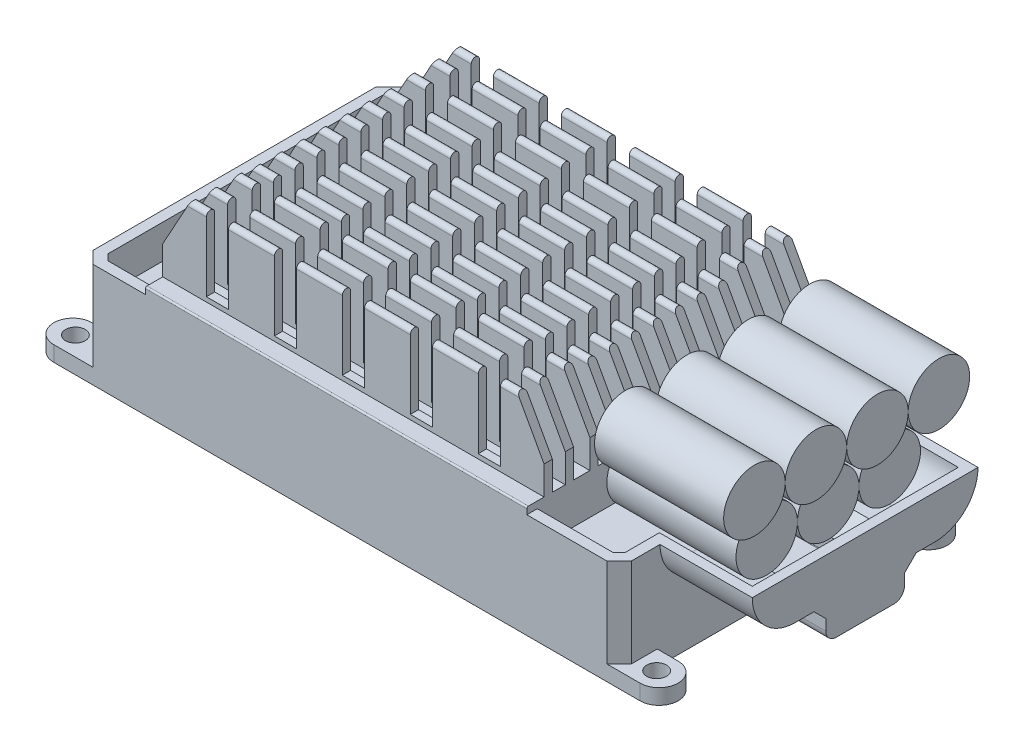
SolidWorks part; units mm, degrees
ref_plane "Front Plane" through (0, 0, 0) normal (0, 0, 1) x (1, 0, 0)
ref_plane "Top Plane" through (0, 0, 0) normal (0, 1, 0) x (1, 0, 0)
ref_plane "Right Plane" through (0, 0, 0) normal (1, 0, 0) x (0, 0, -1)
sketch "Sketch1" plane through (0, 0, 0) normal (0, 1, 0) x (1, 0, 0)
  line L1 (-43.75, -25) -> (43.75, -25)
  line L2 (-43.75, -25) -> (-43.75, 25)
  line L3 (-43.75, 25) -> (43.75, 25)
  line L4 (43.75, -25) -> (43.75, 25)
  line L5 (-43.75, -25) -> (43.75, 25) construction
  line L6 (-43.75, 25) -> (43.75, -25) construction
  point P0 (0, 0)
  dimension "D1" = 87.5
  dimension "D2" = 50
extrude "Boss-Extrude1" add sketch "Sketch1" along normal blind 17
sketch "Sketch2" plane through (0, 0, 0) normal (0, -1, 0) x (1, 0, 0)
  line L0 (43.75, 25) -> (47.15, 25)
  line L1 (47.15, 18.8) -> (43.75, 18.8)
  line L2 (43.75, 25) -> (43.75, -25) construction
  line L3 (43.75, 18.8) -> (43.75, 25)
  line L4 (50.25, 25.3121) -> (50.25, 13.6499) construction
  line L5 (-43.75, 25) -> (-48.15, 25)
  line L6 (-48.15, 18.8) -> (-43.75, 18.8)
  line L7 (-43.75, -25) -> (-43.75, 25) construction
  line L8 (-43.75, 18.8) -> (-43.75, 25)
  line L9 (-51.25, 27.9542) -> (-51.25, 11.7767) construction
  line L10 (-0.5, 36.3188) -> (-0.5, -36.8668) construction
  line L11 (-48.15, 21.9) -> (47.15, 21.9) construction
  arc A0 (47.15, 25) -> (47.15, 18.8) centre (47.15, 21.9) cw
  circle A1 centre (46.75, 21.9) radius 1.6
  arc A2 (-48.15, 25) -> (-48.15, 18.8) centre (-48.15, 21.9) ccw
  circle A3 centre (-47.75, 21.9) radius 1.6
  dimension "D3" = 94.5
  dimension "D5" = 3.2
  dimension "D1" = 6.2
  dimension "D2" = 6.5
  dimension "D4" = 7.5
extrude "Boss-Extrude2" add sketch "Sketch2" against normal blind 2.5
mirror "Mirror5" about plane through (0, 0, 0) normal (0, 0, 1) of "Boss-Extrude2"
chamfer "Chamfer1" distance 2 angle 45 4 edges at (-43.75, 9.75, -25) (43.75, 9.75, -25)
ref_plane "Plane1" through (-33.25, 0, 0) normal (-1, 0, 0) x (0, 0, 1)
sketch "Sketch3" plane through (-33.25, 0, 0) normal (-1, 0, 0) x (0, 0, 1)
  line L0 (-25, 17) -> (0, 17)
  line L1 (0, 17) -> (0, 30.1)
  line L2 (-0.675, 29.425) -> (-0.675, 18.1)
  line L3 (-0.675, 18.1) -> (-2.9, 18.1)
  line L4 (-2.9, 18.1) -> (-2.9, 29.425)
  line L5 (-4.25, 29.425) -> (-4.25, 18.1)
  line L6 (-4.25, 18.1) -> (-6.45, 18.1)
  line L7 (-6.45, 18.1) -> (-6.45, 29.425)
  line L8 (-7.8, 29.425) -> (-7.8, 18.1)
  line L9 (-7.8, 18.1) -> (-9.95, 18.1)
  line L10 (-9.95, 18.1) -> (-9.95, 29.425)
  line L11 (-11.3, 29.425) -> (-11.3, 18.1)
  line L12 (-11.3, 18.1) -> (-13.4, 18.1)
  line L13 (-13.4, 18.1) -> (-13.4, 30.075)
  line L14 (-14.75, 30.075) -> (-14.75, 18.1)
  line L15 (-14.75, 18.1) -> (-17.4, 18.1)
  line L16 (-17.4, 18.1) -> (-17.4, 30.075)
  line L17 (-18.75, 30.075) -> (-18.75, 18.1)
  line L18 (-18.75, 18.1) -> (-20.85, 18.1)
  line L19 (-20.85, 18.1) -> (-20.85, 30.075)
  line L20 (-22.2, 30.075) -> (-22.2, 18.1)
  line L21 (-22.2, 18.1) -> (-24.75, 18.1)
  line L22 (-25, 17.85) -> (-25, 17)
  line L23 (-22.2, 18.1) -> (-20.85, 18.1) construction
  line L24 (-18.75, 18.1) -> (-17.4, 18.1) construction
  line L25 (-14.75, 18.1) -> (-13.4, 18.1) construction
  line L26 (-11.3, 18.1) -> (-9.95, 18.1) construction
  line L27 (-7.8, 18.1) -> (-6.45, 18.1) construction
  line L28 (-4.25, 18.1) -> (-2.9, 18.1) construction
  line L29 (-23, 17) -> (23, 17) construction
  line L30 (-25, 2.5) -> (-25, 17) construction
  line L31 (0, 32.3673) -> (0, 1.3206) construction
  line L32 (25, 17) -> (25, 2.5) construction
  line L33 (-29.0745, 30.75) -> (-4.8916, 30.75) construction
  line L34 (-29.5054, 30.1) -> (10.134, 30.1) construction
  arc A0 (0, 30.1) -> (-0.675, 29.425) centre (0, 29.425) ccw
  arc A1 (-2.9, 29.425) -> (-4.25, 29.425) centre (-3.575, 29.425) ccw
  arc A2 (-6.45, 29.425) -> (-7.8, 29.425) centre (-7.125, 29.425) ccw
  arc A3 (-9.95, 29.425) -> (-11.3, 29.425) centre (-10.625, 29.425) ccw
  arc A4 (-13.4, 30.075) -> (-14.75, 30.075) centre (-14.075, 30.075) ccw
  arc A5 (-17.4, 30.075) -> (-18.75, 30.075) centre (-18.075, 30.075) ccw
  arc A6 (-20.85, 30.075) -> (-22.2, 30.075) centre (-21.525, 30.075) ccw
  arc A7 (-24.75, 18.1) -> (-25, 17.85) centre (-24.75, 17.85) ccw
  dimension "D10" = 0.25
  dimension "D1" = 2.8
  dimension "D2" = 4.8
  dimension "D3" = 1.35
  dimension "D4" = 0.675
  dimension "D5" = 8.8
  dimension "D6" = 12.25
  dimension "D7" = 15.75
  dimension "D8" = 19.3
  dimension "D9" = 1.1
  dimension "D11" = 12.65
  dimension "D12" = 12
extrude "Boss-Extrude3" add sketch "Sketch3" against normal blind 62
mirror "Mirror3" about plane through (0, 0, 0) normal (0, 0, 1) of "Boss-Extrude3"
sketch "Sketch4" plane through (0, 0, -22.2) normal (0, 0, -1) x (-1, 0, 0)
  line L0 (28.85, 30.75) -> (33.25, 22.75)
  line L1 (33.25, 22.75) -> (33.25, 30.75)
  line L2 (33.25, 30.75) -> (28.85, 30.75)
  line L3 (33.25, 30.075) -> (33.25, 18.1) construction
  line L4 (33.25, 30.75) -> (-28.75, 30.75) construction
  line L5 (-28.75, 22.75) -> (-24.35, 30.75)
  line L6 (-24.35, 30.75) -> (-28.75, 30.75)
  line L7 (-28.75, 30.75) -> (-28.75, 22.75)
  line L8 (-28.75, 30.075) -> (-28.75, 18.1) construction
  line L9 (-28.75, 18.1) -> (33.25, 18.1) construction
  line L10 (-21.65, 30.75) -> (-18.05, 30.75)
  line L11 (-21.65, 30.75) -> (-21.65, 18.85)
  line L12 (-21.65, 18.85) -> (-18.05, 18.85)
  line L13 (-18.05, 30.75) -> (-18.05, 18.85)
  line L14 (-10.6, 30.75) -> (-10.6, 18.85)
  line L15 (-10.6, 30.75) -> (-7, 30.75)
  line L16 (-7, 30.75) -> (-7, 18.85)
  line L17 (-10.6, 18.85) -> (-7, 18.85)
  line L18 (0.45, 30.75) -> (0.45, 18.85)
  line L19 (0.45, 30.75) -> (4.05, 30.75)
  line L20 (4.05, 30.75) -> (4.05, 18.85)
  line L21 (0.45, 18.85) -> (4.05, 18.85)
  line L22 (11.5, 30.75) -> (11.5, 18.85)
  line L23 (11.5, 30.75) -> (15.1, 30.75)
  line L24 (15.1, 30.75) -> (15.1, 18.85)
  line L25 (11.5, 18.85) -> (15.1, 18.85)
  line L26 (22.55, 30.75) -> (22.55, 18.85)
  line L27 (22.55, 30.75) -> (26.15, 30.75)
  line L28 (26.15, 30.75) -> (26.15, 18.85)
  line L29 (22.55, 18.85) -> (26.15, 18.85)
  dimension "D1" = 4.4
  dimension "D2" = 8
  dimension "D3" = 7.1
  dimension "D4" = 3.6
  dimension "D5" = 0.75
  dimension "D7" = 7.1
  dimension "D6" = 5
extrude "Cut-Extrude1" cut sketch "Sketch4" against normal through all both and the other way through all
sketch "Sketch5" plane through (43.75, 0, 0) normal (1, 0, 0) x (0, 0, -1)
  line L0 (0, 4.6) -> (0, 17)
  line L1 (-23, 17) -> (23, 17) construction
  line L2 (0, 17) -> (-18.35, 17)
  line L3 (-11.35, 10) -> (-8.3092, 10)
  line L4 (-6.4, 8.0908) -> (-6.4, 6.3)
  line L5 (-4.7, 4.6) -> (0, 4.6)
  line L6 (-11.35, 10) -> (-5.6108, 10) construction
  line L7 (-8.3092, 10) -> (-6.4, 8.0908)
  arc A0 (-18.35, 17) -> (-11.35, 10) centre (-11.35, 17) ccw
  arc A1 (-6.4, 6.3) -> (-4.7, 4.6) centre (-4.7, 6.3) ccw
  dimension "D3" = 1.7
  dimension "D5" = 7
  dimension "D1" = 12.4
  dimension "D2" = 6.4
  dimension "D4" = 45
  dimension "D6" = 18.35
  dimension "D7" = 2.7
extrude "Boss-Extrude4" add sketch "Sketch5" along normal blind 15
mirror "Mirror4" about plane through (0, 0, 0) normal (0, 0, 1) of "Boss-Extrude4"
sketch "Sketch9" plane through (0, 17, 0) normal (0, 1, 0) x (1, 0, 0)
  line L0 (28.75, -23.3) -> (28.75, 23.3)
  line L1 (28.75, 25) -> (28.75, -25) construction
  line L67 (42.05, 18.35) -> (42.05, 22.2958)
  line L68 (42.05, 22.2958) -> (41.0458, 23.3)
  line L69 (41.0458, 23.3) -> (28.75, 23.3)
  line L70 (42.05, 18.35) -> (42.05, 22.2958)
  line L71 (42.05, 22.2958) -> (41.0458, 23.3)
  line L72 (41.0458, 23.3) -> (28.75, 23.3)
  line L73 (42.05, -18.35) -> (42.05, 18.35)
  line L76 (42.05, -22.2958) -> (42.05, -18.35)
  line L77 (41.0458, -23.3) -> (42.05, -22.2958)
  line L78 (28.75, -23.3) -> (41.0458, -23.3)
  line L79 (42.05, -22.2958) -> (42.05, -18.35)
  line L80 (41.0458, -23.3) -> (42.05, -22.2958)
  line L81 (28.75, -23.3) -> (41.0458, -23.3)
  line L85 (-33.25, 23.3) -> (-33.25, -23.3)
  line L90 (-41.0458, -23.3) -> (-33.25, -23.3)
  line L91 (-42.05, -22.2958) -> (-41.0458, -23.3)
  line L92 (-42.05, 22.2958) -> (-42.05, -22.2958)
  line L93 (-41.0458, 23.3) -> (-42.05, 22.2958)
  line L94 (-33.25, 23.3) -> (-41.0458, 23.3)
  line L95 (-41.0458, -23.3) -> (-33.25, -23.3)
  line L96 (-42.05, -22.2958) -> (-41.0458, -23.3)
  line L97 (-42.05, 22.2958) -> (-42.05, -22.2958)
  line L98 (-41.0458, 23.3) -> (-42.05, 22.2958)
  line L99 (-33.25, 23.3) -> (-41.0458, 23.3)
  dimension "D1" = 1.7
  dimension "D2" = 1.7
  dimension "D3" = 1.7
extrude "Cut-Extrude3" cut sketch "Sketch9" against normal blind 5.5
sketch "Sketch8" plane through (58.75, 0, 0) normal (1, 0, 0) x (0, 0, -1)
  line L0 (-16.75, 17) -> (16.75, 17)
  line L15 (7.6464, 11.6) -> (11.35, 11.6)
  line L16 (4.8, 8.7536) -> (7.6464, 11.6)
  line L17 (4.8, 6.3) -> (4.8, 8.7536)
  line L18 (-4.7, 6.2) -> (4.7, 6.2)
  line L19 (-4.8, 8.7536) -> (-4.8, 6.3)
  line L20 (-7.6464, 11.6) -> (-4.8, 8.7536)
  line L21 (-11.35, 11.6) -> (-7.6464, 11.6)
  line L22 (7.6464, 11.6) -> (11.35, 11.6)
  line L23 (4.8, 8.7536) -> (7.6464, 11.6)
  line L24 (4.8, 6.3) -> (4.8, 8.7536)
  line L25 (-4.7, 6.2) -> (4.7, 6.2)
  line L26 (-4.8, 8.7536) -> (-4.8, 6.3)
  line L27 (-7.6464, 11.6) -> (-4.8, 8.7536)
  line L28 (-11.35, 11.6) -> (-7.6464, 11.6)
  arc A9 (11.35, 11.6) -> (16.75, 17) centre (11.35, 17) ccw
  arc A10 (4.7, 6.2) -> (4.8, 6.3) centre (4.7, 6.3) ccw
  arc A11 (-4.8, 6.3) -> (-4.7, 6.2) centre (-4.7, 6.3) ccw
  arc A12 (-16.75, 17) -> (-11.35, 11.6) centre (-11.35, 17) ccw
  arc A13 (11.35, 11.6) -> (16.75, 17) centre (11.35, 17) ccw
  arc A14 (4.7, 6.2) -> (4.8, 6.3) centre (4.7, 6.3) ccw
  arc A15 (-4.8, 6.3) -> (-4.7, 6.2) centre (-4.7, 6.3) ccw
  arc A16 (-16.75, 17) -> (-11.35, 11.6) centre (-11.35, 17) ccw
  dimension "D1" = 1.6
extrude "Cut-Extrude2" cut sketch "Sketch8" against normal up to surface (15.1 mm away) from offset 1.6 up to face at (42.05, 14.25, 0) offset against normal yes
sketch "Sketch6" plane through (58.75, 0, 0) normal (1, 0, 0) x (0, 0, -1)
  line L0 (0, 0) -> (0, 41.4393) construction
  line L1 (-27.496, 32.5) -> (13.9475, 32.5) construction
  line L2 (-18.8, 0) -> (18.8, 0) construction
  circle A0 centre (-15, 27.5) radius 5
  dimension "D1" = 10
  dimension "D2" = 15
  dimension "D3" = 32.5
extrude "Boss-Extrude5" add sketch "Sketch6" against normal blind 21 from offset 3 separate body offset against normal yes
pattern_linear "LPattern1" count 4 spacing 10 along (0, 0, -1) of "Boss-Extrude5"
sketch "Sketch7" plane through (58.75, 0, 0) normal (1, 0, 0) x (0, 0, -1)
  line L0 (-18.8, 0) -> (18.8, 0) construction
  line L1 (0, 0) -> (0, 40.9104) construction
  line L2 (-10, 38.401) -> (-10, 18) construction
  line L3 (-10, 18) -> (10, 18) construction
  circle A0 centre (-10, 18) radius 4.9995
  circle A2 centre (-15, 27.5) radius 5 construction
  circle A3 centre (0, 18) radius 4.9995
  circle A4 centre (10, 18) radius 4.9995
  dimension "D2" = 9.999
  dimension "D1" = 18
  dimension "D3" = 3
extrude "Boss-Extrude6" add sketch "Sketch7" against normal blind 21 from offset 6
